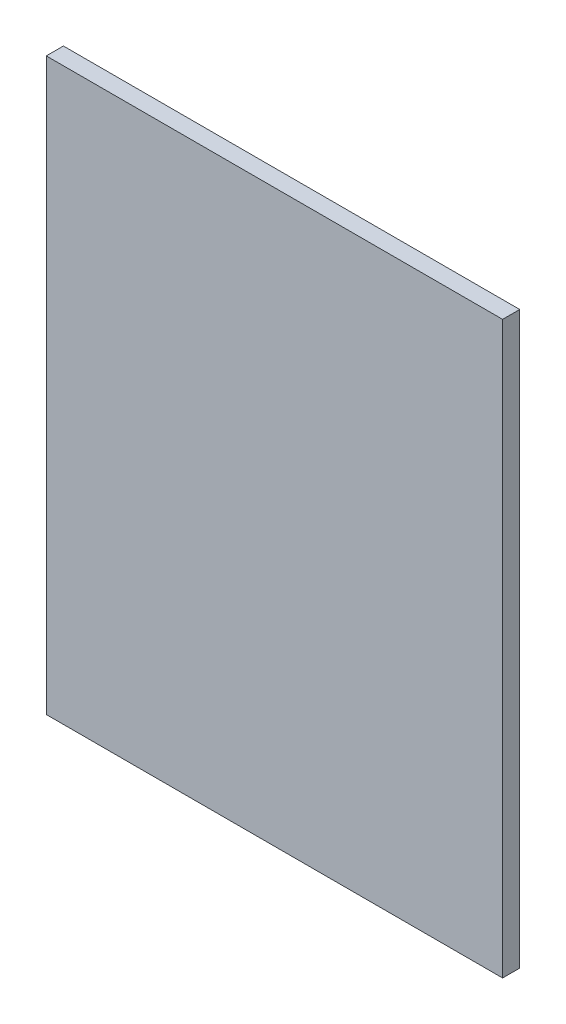
SolidWorks part; units mm, degrees
ref_plane "Plano frontal" through (0, 0, 0) normal (0, 0, 1) x (1, 0, 0)
ref_plane "Plano superior" through (0, 0, 0) normal (0, 1, 0) x (1, 0, 0)
ref_plane "Plano direito" through (0, 0, 0) normal (1, 0, 0) x (0, 0, -1)
sketch "Esboço1" plane through (0, 0, 0) normal (0, 0, 1) x (1, 0, 0)
  line L1 (-24.4396, 11.1209) -> (55.5604, 11.1209)
  line L2 (-24.4396, 11.1209) -> (-24.4396, -88.8791)
  line L3 (-24.4396, -88.8791) -> (55.5604, -88.8791)
  line L4 (55.5604, 11.1209) -> (55.5604, -88.8791)
  dimension "D1" = 80
  dimension "D2" = 100
extrude "Ressalto-extrusão1" add sketch "Esboço1" along normal blind 3
